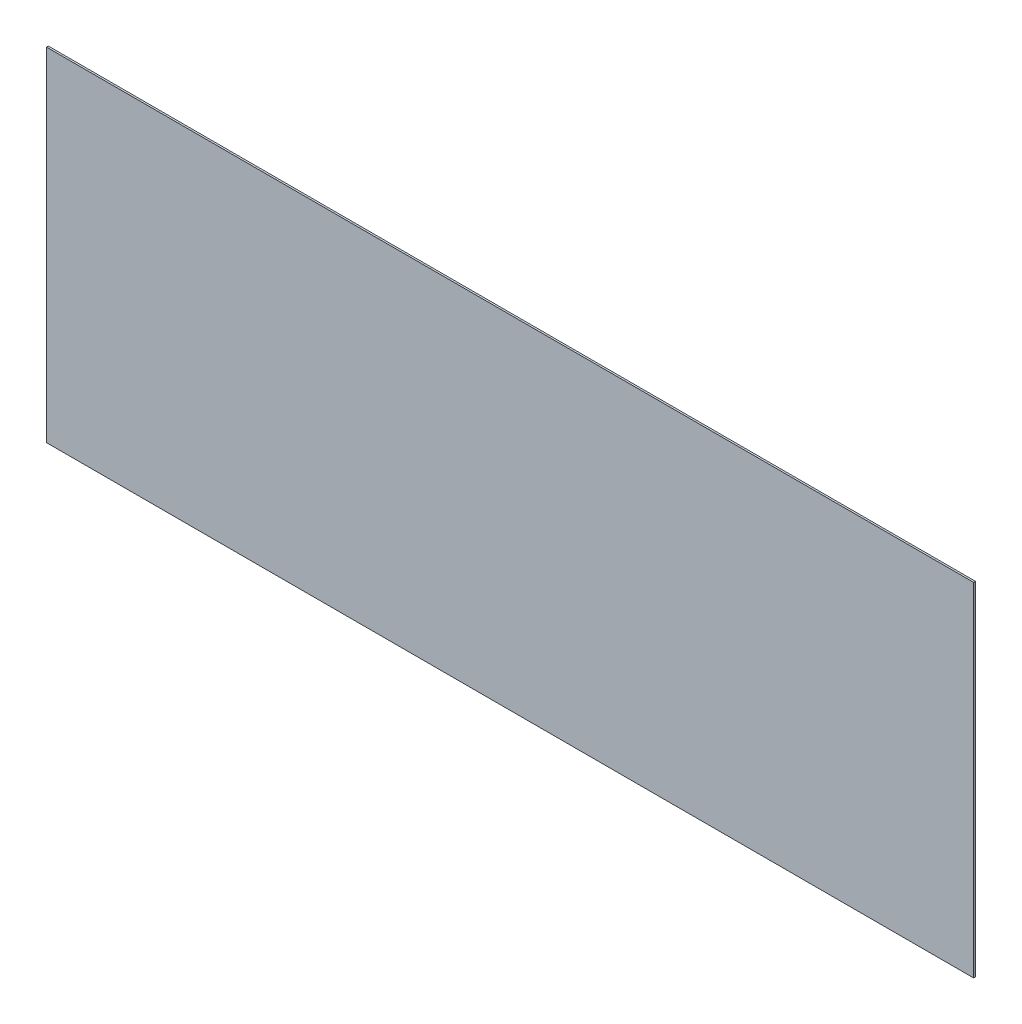
SolidWorks part; units mm, degrees
ref_plane "Front Plane" through (0, 0, 0) normal (0, 0, 1) x (1, 0, 0)
ref_plane "Top Plane" through (0, 0, 0) normal (0, 1, 0) x (1, 0, 0)
ref_plane "Right Plane" through (0, 0, 0) normal (1, 0, 0) x (0, 0, -1)
sketch "Sketch1" plane through (0, 0, 0) normal (0, 0, 1) x (1, 0, 0)
  line L1 (790.575, -292.1) -> (-790.575, -292.1)
  line L2 (790.575, -292.1) -> (790.575, 292.1)
  line L3 (790.575, 292.1) -> (-790.575, 292.1)
  line L4 (-790.575, -292.1) -> (-790.575, 292.1)
  line L5 (790.575, -292.1) -> (-790.575, 292.1) construction
  line L6 (790.575, 292.1) -> (-790.575, -292.1) construction
  point P0 (0, 0)
  dimension "D1" = 1581.15
  dimension "D2" = 584.2
extrude "Boss-Extrude1" add sketch "Sketch1" along normal blind 3.175
